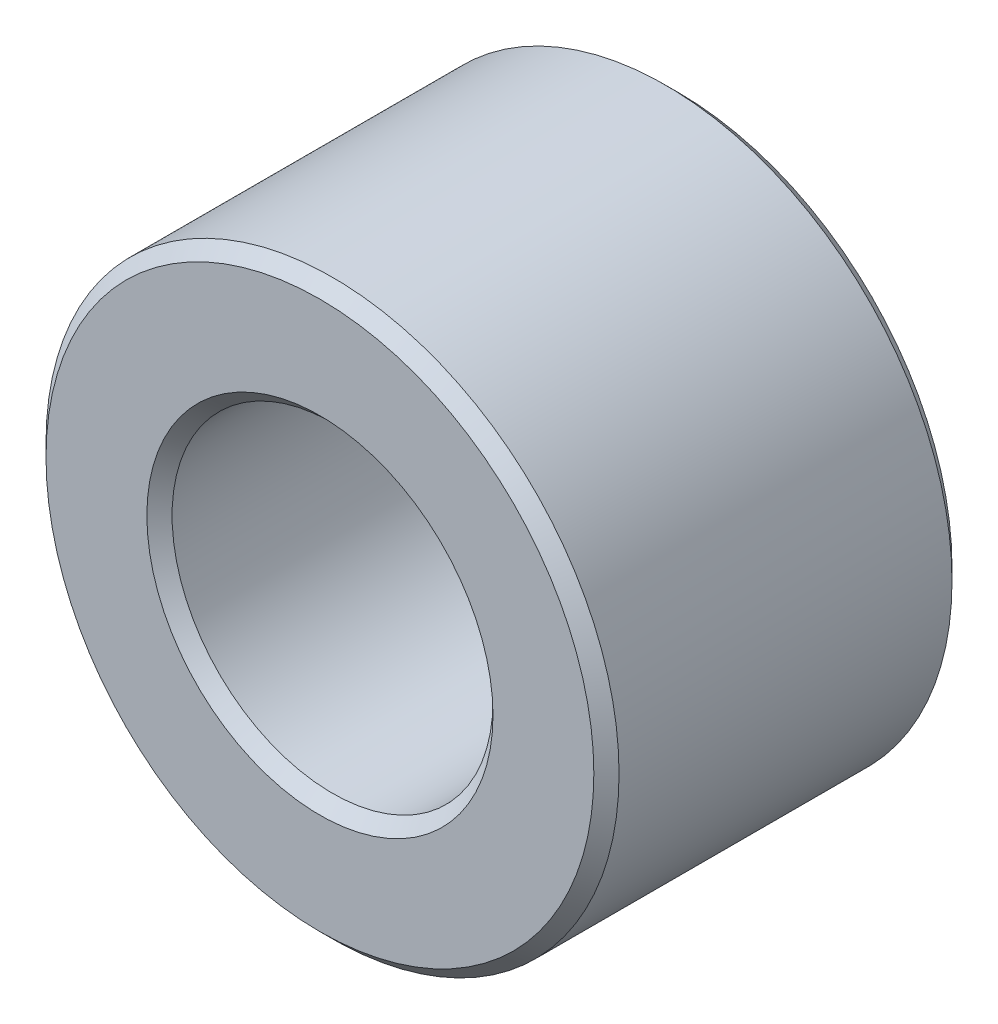
SolidWorks part; units mm, degrees
ref_plane "Front Plane" through (0, 0, 0) normal (0, 0, 1) x (1, 0, 0)
ref_plane "Top Plane" through (0, 0, 0) normal (0, 1, 0) x (1, 0, 0)
ref_plane "Right Plane" through (0, 0, 0) normal (1, 0, 0) x (0, 0, -1)
sketch "Sketch1" plane through (0, 0, 0) normal (0, 0, 1) x (1, 0, 0)
  circle A0 centre (0, 0) radius 3.175 construction
  circle A1 centre (0, 0) radius 1.778 construction
  point P4 (0, 3.175)
  dimension "ID" = 3.556
  dimension "OD" = 6.35
sketch "Sketch2" plane through (0, 0, 0) normal (1, 0, 0) x (0, 0, -1)
  line L0 (-1.9844, 3.175) -> (1.9844, 3.175) construction
  dimension "Length" = 3.9688
sketch "Sketch3" plane through (0, 0, 0) normal (0, 0, 1) x (1, 0, 0)
  circle A0 centre (0, 0) radius 1.778 construction
  circle A1 centre (0, 0) radius 3.175 construction
  circle A2 centre (0, 0) radius 1.778
  circle A3 centre (0, 0) radius 3.175
extrude "Boss-Extrude1" add sketch "Sketch3" against normal up to vertex (1.9844 mm away) and the other way up to vertex (1.9844 mm away) up to point (0, 3.175, -1.9844) other way up to point (0, 3.175, 1.9844)
chamfer "Chamfer1" distance 0.1397 angle 45 4 edges at (3.175, 0, 1.9844) (3.175, 0, -1.9844) (1.778, 0, 1.9844) (1.778, 0, -1.9844)
equation "\"D1@Chamfer1\"=(\"OD@Sketch1\"-\"ID@Sketch1\")*0.05"
